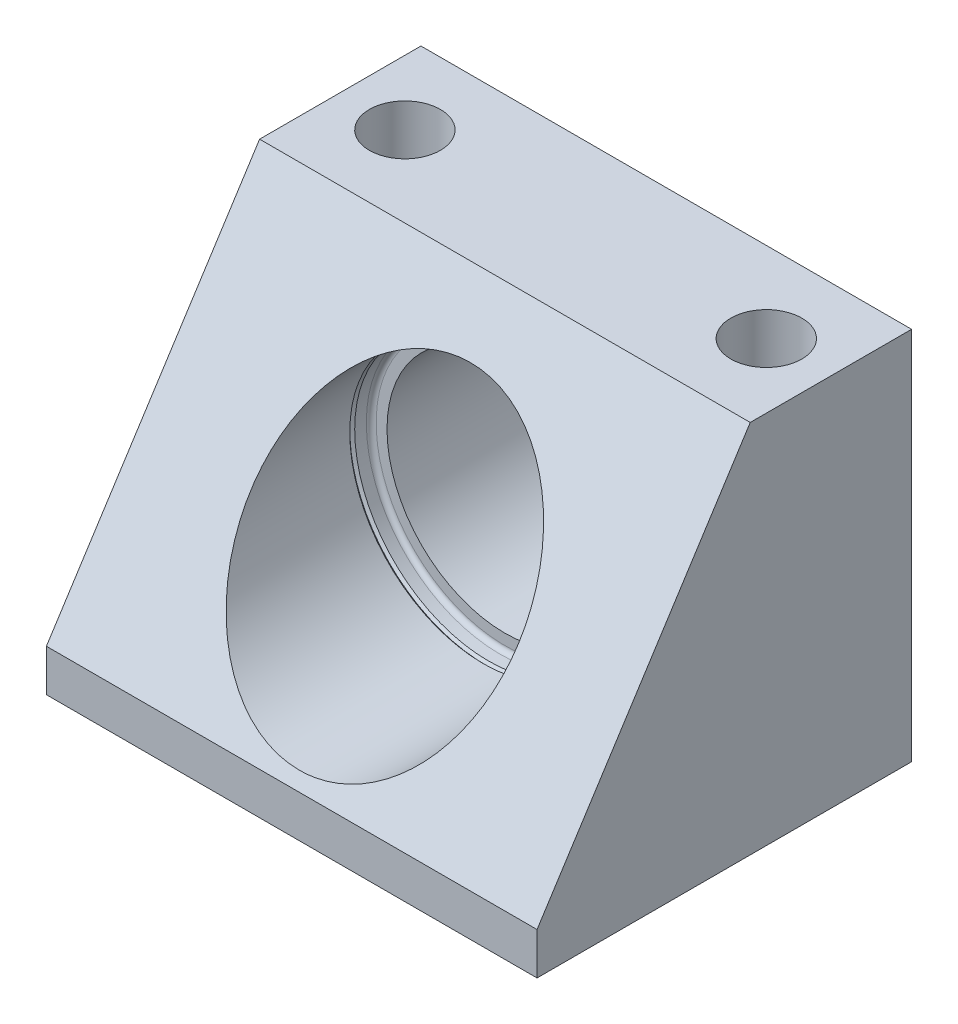
SolidWorks part; units mm, degrees
material "Alloy Steel"
ref_plane "Front Plane" through (0, 0, 0) normal (0, 0, 1) x (1, 0, 0)
ref_plane "Top Plane" through (0, 0, 0) normal (0, 1, 0) x (1, 0, 0)
ref_plane "Right Plane" through (0, 0, 0) normal (1, 0, 0) x (0, 0, -1)
sketch "Sketch1" plane through (0, 0, 0) normal (0, 0, 1) x (1, 0, 0)
  line L0 (37.9984, 0) -> (37.9984, 58.0136) construction
  line L1 (0, 58.0136) -> (75.9968, 58.0136)
  line L2 (0, 58.0136) -> (0, 0)
  line L3 (0, 0) -> (75.9968, 0)
  line L4 (75.9968, 58.0136) -> (75.9968, 0)
  circle A0 centre (37.9984, 29.0068) radius 18.2625
  dimension "D4" = 36.525
  dimension "D1" = 75.9968
  dimension "D2" = 58.0136
  dimension "D3" = 29.0068
extrude "Extrude1" add sketch "Sketch1" against normal blind 58.0136
sketch "Sketch2" plane through (75.9968, 0, 0) normal (1, 0, 0) x (0, 0, -1)
  line L0 (0, 58.0136) -> (33.02, 58.0136)
  line L3 (58.0136, 58.0136) -> (0, 58.0136) construction
  line L4 (33.02, 58.0136) -> (0, 6.5024)
  line L5 (0, 0) -> (0, 58.0136) construction
  line L6 (0, 6.5024) -> (0, 58.0136)
  line L7 (58.0136, 0) -> (58.0136, 58.0136) construction
  line L8 (58.0136, 0) -> (0, 0) construction
  dimension "D2" = 6.5024
  dimension "D1" = 24.9936
extrude "Cut-Extrude1" cut sketch "Sketch2" against normal through all
sketch "Sketch3" plane through (0, 0, 0) normal (0, 0, -1) x (-1, 0, 0)
  circle A0 centre (-37.9984, 29.0068) radius 20.701
  dimension "D1" = 41.402
extrude "Cut-Extrude2" cut sketch "Sketch3" along normal offset from surface (33.02 mm away) 24.9936 up to face at (56.2609, 29.0068, -58.0136)
fillet "Fillet1" radius 0.762 1 edges at (58.6994, 29.0068, -33.02)
hole_wizard "Hole1" positions "Sketch5" profile "Sketch4" legacy end condition up to next
sketch "Sketch5" plane through (0, 58.0136, 0) normal (0, 1, 0) x (-1, 0, 0)
  line L0 (-75.9968, -58.0136) -> (-75.9968, -33.02) construction
  line L2 (-75.9968, -58.0136) -> (0, -58.0136) construction
  point P0 (-10.0076, -45.5168)
  point P1 (-65.9892, -45.5168)
  dimension "D1" = 10.0076
  dimension "D2" = 12.4968
  dimension "D3" = 55.9816
sketch "Sketch4" plane through (10.0076, 58.0136, -45.5168) normal (1, 0, 0) x (0, 0, 1)
  line L0 (0, 0) -> (0, 58.0136)
  line L1 (0, 58.0136) -> (5.4991, 58.0136)
  line L2 (5.4991, 58.0136) -> (5.4991, 0)
  line L3 (5.4991, 0) -> (0, 0)
  line L4 (0, 110) -> (0, -10) construction
  dimension "Diameter" = 10.9982
  dimension "Depth" = 58.0136
ref_plane "Plane1" through (0, 29.0068, 0) normal (0, 1, 0) x (-1, 0, 0)
sketch "Sketch6" plane through (0, 29.0068, 0) normal (0, 1, 0) x (-1, 0, 0)
  line L0 (-17.2974, -29.6926) -> (-17.2974, -30.4546)
  line L1 (-17.2974, -32.258) -> (-17.2974, -14.4259) construction
  line L2 (-17.2974, -30.4546) -> (-16.9164, -30.0736)
  line L3 (-16.9164, -30.0736) -> (-17.2974, -29.6926)
  line L4 (-37.9984, 17.5081) -> (-37.9984, -67.5449) construction
  line L5 (-37.9984, -58.0136) -> (-37.9984, -33.02) construction
  line L6 (-75.9968, -58.0136) -> (0, -58.0136) construction
  line L7 (-19.7359, -56.8451) -> (-19.7359, -58.0136)
  line L9 (-19.7359, -58.0136) -> (-18.5674, -58.0136)
  line L10 (-18.5674, -58.0136) -> (-19.7359, -56.8451)
  line L12 (-19.7359, -58.0136) -> (-19.7359, -33.02) construction
  dimension "D1" = 90
  dimension "D2" = 45
  dimension "D3" = 0.762
  dimension "D4" = 27.94
  dimension "D5" = 45
  dimension "D6" = 38.862
revolve "Cut-Revolve1" cut sketch "Sketch6" angle 360 about L4
